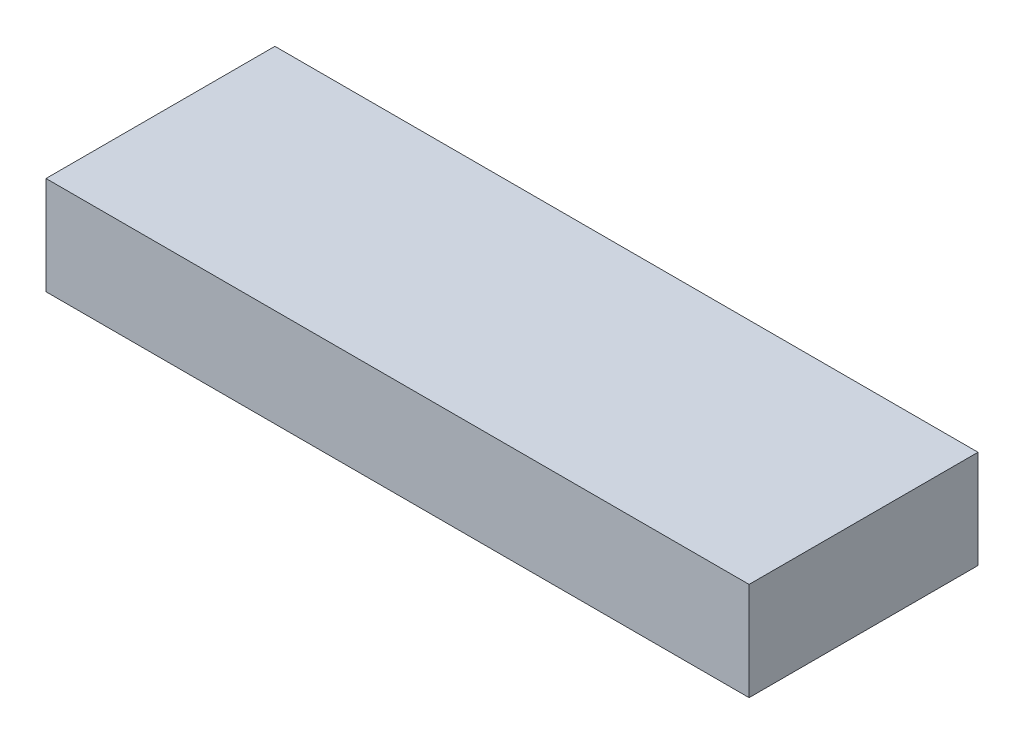
SolidWorks part; units mm, degrees
ref_plane "Front Plane" through (0, 0, 0) normal (0, 0, 1) x (1, 0, 0)
ref_plane "Top Plane" through (0, 0, 0) normal (0, 1, 0) x (1, 0, 0)
ref_plane "Right Plane" through (0, 0, 0) normal (1, 0, 0) x (0, 0, -1)
sketch "Sketch1" plane through (0, 0, 0) normal (0, 1, 0) x (1, 0, 0)
  line L1 (0, 0) -> (273.05, 0)
  line L2 (0, 0) -> (0, -88.9)
  line L3 (0, -88.9) -> (273.05, -88.9)
  line L4 (273.05, 0) -> (273.05, -88.9)
extrude "Boss-Extrude1" add sketch "Sketch1" along normal blind 38.1
sketch "Sketch2" plane through (0, 38.1, 0) normal (0, 1, 0) x (1, 0, 0)
  line L0 (0, -44.45) -> (91.0167, -44.45) construction
  line L1 (0, 0) -> (0, -88.9) construction
  line L2 (91.0167, -44.45) -> (182.0333, -44.45) construction
  line L3 (182.0333, -44.45) -> (273.05, -44.45) construction
  line L4 (273.05, -88.9) -> (273.05, 0) construction
  line L5 (91.0167, 0) -> (91.0167, -88.9) construction
  line L6 (273.05, 0) -> (0, 0) construction
  line L7 (0, -88.9) -> (273.05, -88.9) construction
  line L8 (182.0333, 0) -> (182.0333, -88.9) construction
sketch "Sketch3" plane through (0, 0, 0) normal (0, -1, 0) x (1, 0, 0)
  line L0 (0, 44.45) -> (91.0167, 44.45) construction
  line L1 (91.0167, 44.45) -> (182.0333, 44.45) construction
  line L2 (182.0333, 44.45) -> (273.05, 44.45) construction
  line L3 (91.0167, 88.9) -> (91.0167, 0) construction
  line L4 (182.0333, 88.9) -> (182.0333, 0) construction
